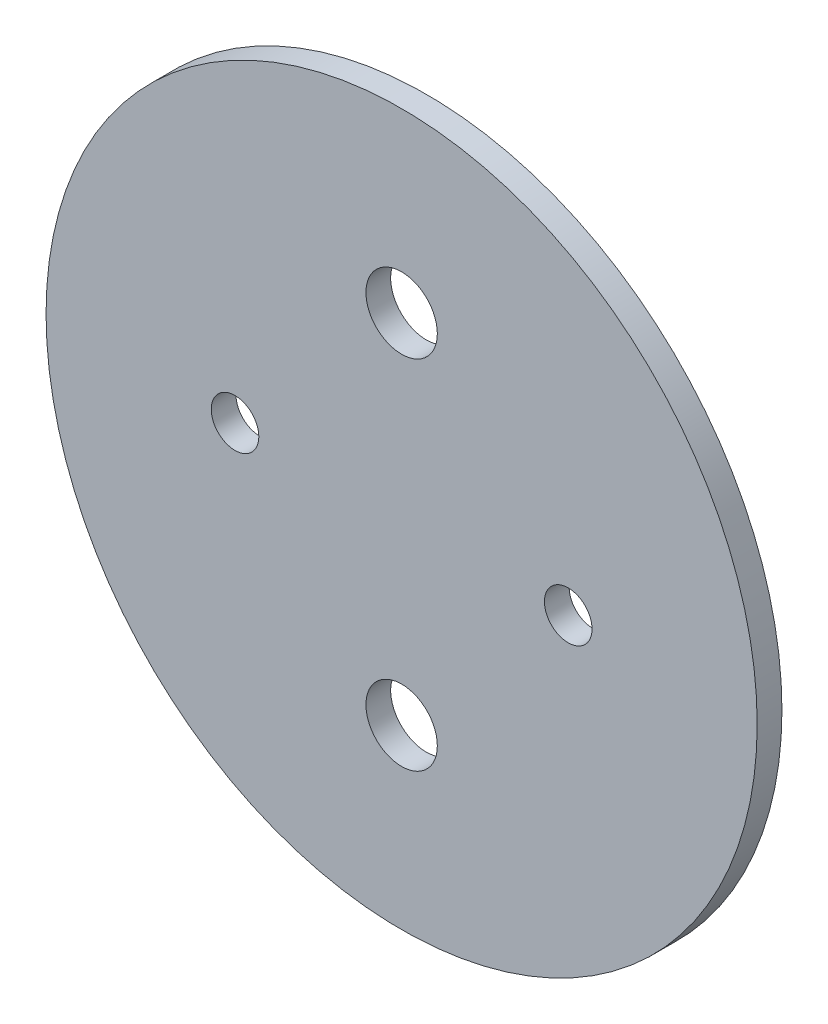
SolidWorks part; units mm, degrees
ref_plane "Front Plane" through (0, 0, 0) normal (0, 0, 1) x (1, 0, 0)
ref_plane "Top Plane" through (0, 0, 0) normal (0, 1, 0) x (1, 0, 0)
ref_plane "Right Plane" through (0, 0, 0) normal (1, 0, 0) x (0, 0, -1)
sketch "Sketch1" plane through (0, 0, 0) normal (0, 0, 1) x (1, 0, 0)
  line L0 (-22.225, 0) -> (22.225, 0) construction
  line L1 (0, 23.8125) -> (0, -23.8125) construction
  circle A0 centre (0, 0) radius 47.4345
  circle A1 centre (-22.225, 0) radius 3.175
  circle A2 centre (22.225, 0) radius 3.175
  circle A3 centre (0, -23.8125) radius 4.7625
  circle A4 centre (0, 23.8125) radius 4.7625
  point P3 (0, 0)
  point P12 (0, 0)
  dimension "D1" = 94.869
  dimension "D3" = 6.35
  dimension "D5" = 9.525
  dimension "D2" = 44.45
  dimension "D4" = 47.625
extrude "Boss-Extrude1" add sketch "Sketch1" along normal blind 3.302
